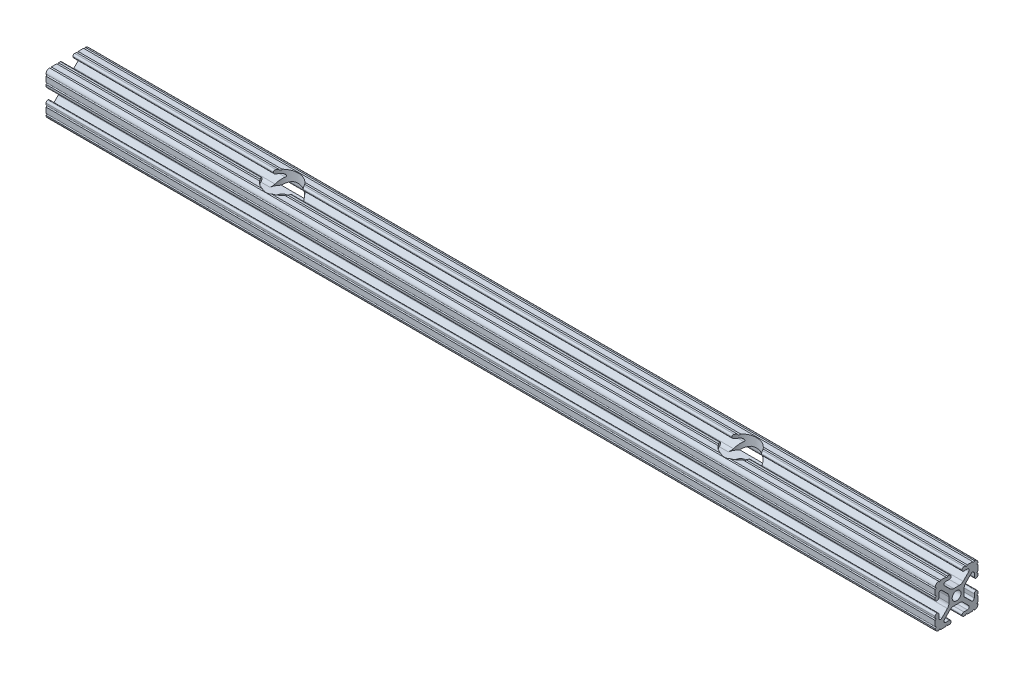
SolidWorks part; units mm, degrees
material "6061-T6 (SS)"
ref_plane "Front Plane" through (0, 0, 0) normal (0, 0, 1) x (1, 0, 0)
ref_plane "Top Plane" through (0, 0, 0) normal (0, 1, 0) x (1, 0, 0)
ref_plane "Right Plane" through (0, 0, 0) normal (1, 0, 0) x (0, 0, -1)
sketch "Sketch1" plane through (0, 0, 0) normal (1, 0, 0) x (0, 0, -1)
  line L0 (6.3331, -12.7) -> (9.5504, -12.7)
  line L1 (12.7, -9.5504) -> (12.7, -6.3331)
  line L2 (12.7, -5.3171) -> (12.7, -4.2875)
  line L3 (11.651, -3.2385) -> (11.5392, -3.2385)
  line L4 (10.4902, -4.2875) -> (10.4902, -6.4021)
  line L5 (8.7371, -7.1294) -> (4.5085, -2.9104)
  line L6 (4.5085, -2.9104) -> (4.5085, 1.5932)
  line L7 (5.441, 3.8408) -> (8.7371, 7.1294)
  line L8 (10.4902, 6.4021) -> (10.4902, 4.2875)
  line L9 (11.5392, 3.2385) -> (11.651, 3.2385)
  line L10 (12.7, 4.2875) -> (12.7, 5.3171)
  line L11 (12.7, 6.3331) -> (12.7, 9.5504)
  line L12 (9.5504, 12.7) -> (6.3331, 12.7)
  line L13 (5.3171, 12.7) -> (4.2875, 12.7)
  line L14 (3.2385, 11.651) -> (3.2385, 11.5392)
  line L15 (4.2875, 10.4902) -> (6.4768, 10.4902)
  line L16 (7.207, 8.7244) -> (3.8983, 5.4232)
  line L17 (1.6558, 4.4958) -> (-1.6558, 4.4958)
  line L18 (-3.8983, 5.4232) -> (-7.207, 8.7244)
  line L19 (-6.4768, 10.4902) -> (-4.2875, 10.4902)
  line L20 (-3.2385, 11.5392) -> (-3.2385, 11.651)
  line L21 (-4.2875, 12.7) -> (-5.3171, 12.7)
  line L22 (-6.3331, 12.7) -> (-9.5504, 12.7)
  line L23 (-12.7, 9.5504) -> (-12.7, 6.3331)
  line L24 (-12.7, 5.3171) -> (-12.7, 4.2875)
  line L25 (-11.651, 3.2385) -> (-11.5392, 3.2385)
  line L26 (-10.4902, 4.2875) -> (-10.4902, 6.4021)
  line L27 (-8.7371, 7.1294) -> (-5.441, 3.8408)
  line L28 (-4.5085, 1.5932) -> (-4.5085, -1.5932)
  line L29 (-5.441, -3.8408) -> (-8.7371, -7.1294)
  line L30 (-10.4902, -6.4021) -> (-10.4902, -4.2875)
  line L31 (-11.5392, -3.2385) -> (-11.651, -3.2385)
  line L32 (-12.7, -4.2875) -> (-12.7, -5.3171)
  line L33 (-12.7, -6.3331) -> (-12.7, -9.5504)
  line L34 (-9.5504, -12.7) -> (-6.3331, -12.7)
  line L35 (-5.3171, -12.7) -> (-4.2875, -12.7)
  line L36 (-3.2385, -11.651) -> (-3.2385, -11.5392)
  line L37 (-4.2875, -10.4902) -> (-6.4164, -10.4902)
  line L38 (-7.1797, -8.6452) -> (-3.9523, -5.4237)
  line L39 (-1.7093, -4.4958) -> (1.7093, -4.4958)
  line L40 (3.9523, -5.4237) -> (7.1797, -8.6452)
  line L41 (6.4164, -10.4902) -> (4.2875, -10.4902)
  line L42 (3.2385, -11.5392) -> (3.2385, -11.651)
  line L43 (4.2875, -12.7) -> (5.3171, -12.7)
  circle A0 centre (0, 0) radius 2.6035
  arc A1 (6.3331, -12.7) -> (5.3171, -12.7) centre (5.8251, -12.7) ccw
  arc A2 (10.5664, -12.6998) -> (9.5504, -12.7) centre (10.0584, -12.7) ccw
  arc A3 (10.5664, -12.6998) -> (12.6998, -10.5664) centre (10.5918, -10.5918) ccw
  arc A4 (12.7, -9.5504) -> (12.6998, -10.5664) centre (12.7, -10.0584) ccw
  arc A5 (12.7, -5.3171) -> (12.7, -6.3331) centre (12.7, -5.8251) ccw
  arc A6 (12.7, -4.2875) -> (11.651, -3.2385) centre (11.651, -4.2875) ccw
  arc A7 (11.5392, -3.2385) -> (10.4902, -4.2875) centre (11.5392, -4.2875) ccw
  arc A8 (8.7371, -7.1294) -> (10.4902, -6.4021) centre (9.4628, -6.4021) ccw
  arc A9 (5.441, 3.8408) -> (4.5085, 1.5932) centre (7.6835, 1.5932) ccw
  arc A10 (10.4902, 6.4021) -> (8.7371, 7.1294) centre (9.4628, 6.4021) ccw
  arc A11 (10.4902, 4.2875) -> (11.5392, 3.2385) centre (11.5392, 4.2875) ccw
  arc A12 (11.651, 3.2385) -> (12.7, 4.2875) centre (11.651, 4.2875) ccw
  arc A13 (12.7, 6.3331) -> (12.7, 5.3171) centre (12.7, 5.8251) ccw
  arc A14 (12.6998, 10.5664) -> (12.7, 9.5504) centre (12.7, 10.0584) ccw
  arc A15 (12.6998, 10.5664) -> (10.5664, 12.6998) centre (10.5918, 10.5918) ccw
  arc A16 (9.5504, 12.7) -> (10.5664, 12.6998) centre (10.0584, 12.7) ccw
  arc A17 (5.3171, 12.7) -> (6.3331, 12.7) centre (5.8251, 12.7) ccw
  arc A18 (4.2875, 12.7) -> (3.2385, 11.651) centre (4.2875, 11.651) ccw
  arc A19 (3.2385, 11.5392) -> (4.2875, 10.4902) centre (4.2875, 11.5392) ccw
  arc A20 (7.207, 8.7244) -> (6.4768, 10.4902) centre (6.4768, 9.4563) ccw
  arc A21 (1.6558, 4.4958) -> (3.8983, 5.4232) centre (1.6558, 7.6708) ccw
  arc A22 (-3.8983, 5.4232) -> (-1.6558, 4.4958) centre (-1.6558, 7.6708) ccw
  arc A23 (-6.4768, 10.4902) -> (-7.207, 8.7244) centre (-6.4768, 9.4563) ccw
  arc A24 (-4.2875, 10.4902) -> (-3.2385, 11.5392) centre (-4.2875, 11.5392) ccw
  arc A25 (-3.2385, 11.651) -> (-4.2875, 12.7) centre (-4.2875, 11.651) ccw
  arc A26 (-6.3331, 12.7) -> (-5.3171, 12.7) centre (-5.8251, 12.7) ccw
  arc A27 (-10.5664, 12.6998) -> (-9.5504, 12.7) centre (-10.0584, 12.7) ccw
  arc A28 (-10.5664, 12.6998) -> (-12.6998, 10.5664) centre (-10.5918, 10.5918) ccw
  arc A29 (-12.7, 9.5504) -> (-12.6998, 10.5664) centre (-12.7, 10.0584) ccw
  arc A30 (-12.7, 5.3171) -> (-12.7, 6.3331) centre (-12.7, 5.8251) ccw
  arc A31 (-12.7, 4.2875) -> (-11.651, 3.2385) centre (-11.651, 4.2875) ccw
  arc A32 (-11.5392, 3.2385) -> (-10.4902, 4.2875) centre (-11.5392, 4.2875) ccw
  arc A33 (-8.7371, 7.1294) -> (-10.4902, 6.4021) centre (-9.4628, 6.4021) ccw
  arc A34 (-4.5085, 1.5932) -> (-5.441, 3.8408) centre (-7.6835, 1.5932) ccw
  arc A35 (-5.441, -3.8408) -> (-4.5085, -1.5932) centre (-7.6835, -1.5932) ccw
  arc A36 (-10.4902, -6.4021) -> (-8.7371, -7.1294) centre (-9.4628, -6.4021) ccw
  arc A37 (-10.4902, -4.2875) -> (-11.5392, -3.2385) centre (-11.5392, -4.2875) ccw
  arc A38 (-11.651, -3.2385) -> (-12.7, -4.2875) centre (-11.651, -4.2875) ccw
  arc A39 (-12.7, -6.3331) -> (-12.7, -5.3171) centre (-12.7, -5.8251) ccw
  arc A40 (-12.6998, -10.5664) -> (-12.7, -9.5504) centre (-12.7, -10.0584) ccw
  arc A41 (-12.6998, -10.5664) -> (-10.5664, -12.6998) centre (-10.5918, -10.5918) ccw
  arc A42 (-9.5504, -12.7) -> (-10.5664, -12.6998) centre (-10.0584, -12.7) ccw
  arc A43 (-5.3171, -12.7) -> (-6.3331, -12.7) centre (-5.8251, -12.7) ccw
  arc A44 (-4.2875, -12.7) -> (-3.2385, -11.651) centre (-4.2875, -11.651) ccw
  arc A45 (-3.2385, -11.5392) -> (-4.2875, -10.4902) centre (-4.2875, -11.5392) ccw
  arc A46 (-7.1797, -8.6452) -> (-6.4164, -10.4902) centre (-6.4164, -9.4098) ccw
  arc A47 (-1.7093, -4.4958) -> (-3.9523, -5.4237) centre (-1.7093, -7.6708) ccw
  arc A48 (3.9523, -5.4237) -> (1.7093, -4.4958) centre (1.7093, -7.6708) ccw
  arc A49 (6.4164, -10.4902) -> (7.1797, -8.6452) centre (6.4164, -9.4098) ccw
  arc A50 (4.2875, -10.4902) -> (3.2385, -11.5392) centre (4.2875, -11.5392) ccw
  arc A51 (3.2385, -11.651) -> (4.2875, -12.7) centre (4.2875, -11.651) ccw
extrude "Boss-Extrude1" add sketch "Sketch1" along normal mid plane 527.05
hole_wizard "CBORE for #0 Binding Head Machine Screw1" positions "Sketch2" profile "Sketch4" counterbore size "#0" standard "ANSI Inch" end condition through all
sketch "Sketch2" plane through (0, 12.7, 0) normal (0, 1, 0) x (1, 0, 0)
  circle A0 centre (-135.8588, -0.381) radius 2.413 construction
  circle A1 centre (135.8588, -0.381) radius 2.413 construction
  point P0 (-135.8588, -0.381)
  point P2 (135.8588, -0.381)
sketch "Sketch4" plane through (-135.8588, 12.7, 0.381) normal (1, 0, 0) x (0, 0, 1)
  line L0 (0, 0) -> (0, 25.4)
  line L1 (0, 25.4) -> (3.175, 25.4)
  line L3 (3.175, 25.4) -> (3.175, 8.2042)
  line L4 (3.175, 8.2042) -> (9.525, 8.2042)
  line L5 (9.525, 8.2042) -> (9.525, 0)
  line L7 (9.525, 0) -> (0, 0)
  line L11 (0, -6.35) -> (0, 107.95) construction
  dimension "Thru Hole Dia." = 6.35
  dimension "Thru Hole Depth" = 25.4
  dimension "C'Bore Dia." = 19.05
  dimension "C'Bore Depth" = 8.2042
